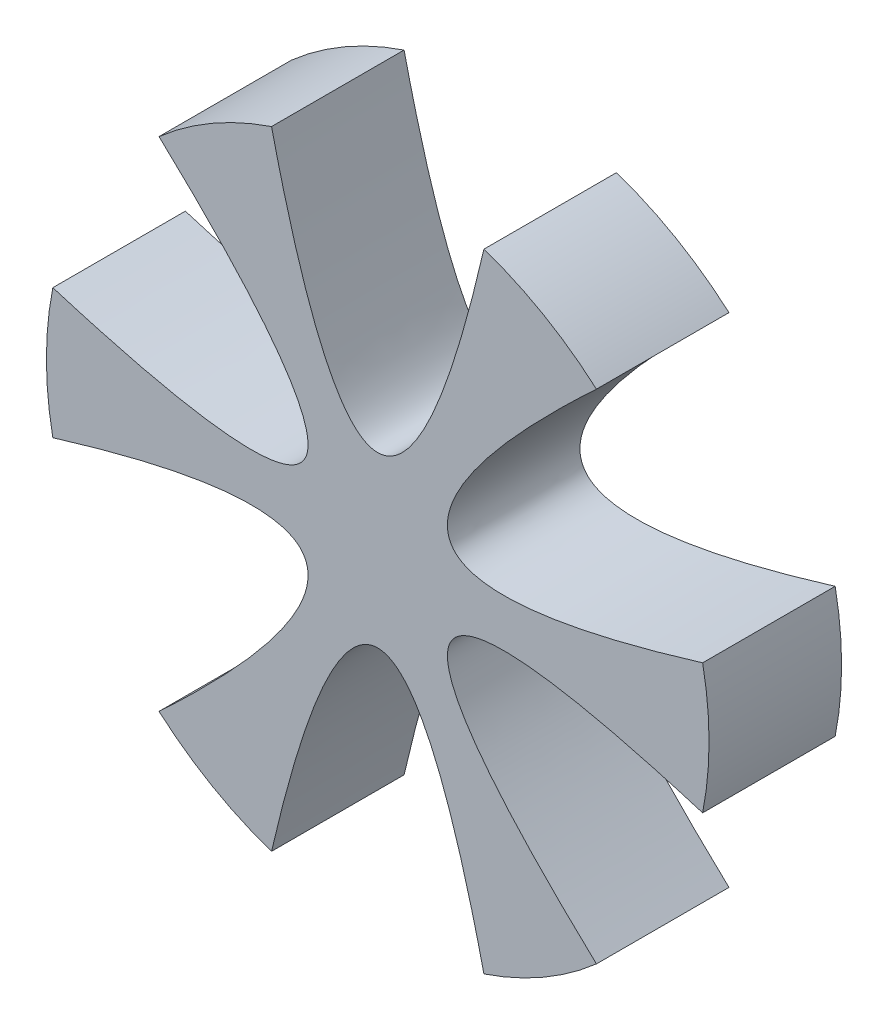
SolidWorks part; units mm, degrees
ref_plane "Front Plane" through (0, 0, 0) normal (0, 0, 1) x (1, 0, 0)
ref_plane "Top Plane" through (0, 0, 0) normal (0, 1, 0) x (1, 0, 0)
ref_plane "Right Plane" through (0, 0, 0) normal (1, 0, 0) x (0, 0, -1)
sketch "Sketch2" plane through (0, 0, 0) normal (0, 0, 1) x (1, 0, 0)
  circle A0 centre (0, 0) radius 38.1
  dimension "D1" = 76.2
extrude "Boss-Extrude1" add sketch "Sketch2" along normal blind 2.54
sketch "Sketch3" plane through (0, 0, 2.54) normal (0, 0, 1) x (1, 0, 0)
  line L0 (0, 0) -> (0, 57.9417) construction
  arc A0 (-37.3604, 7.4707) -> (-37.3604, -7.4707) centre (0, 0) ccw
  arc A1 (-12.2104, 36.0904) -> (-25.15, 28.6197) centre (0, 0) ccw
  circle A2 centre (0, 0) radius 38.1 construction
  arc A3 (25.15, 28.6197) -> (12.2104, 36.0904) centre (0, 0) ccw
  arc A4 (37.3604, -7.4707) -> (37.3604, 7.4707) centre (0, 0) ccw
  arc A5 (12.2104, -36.0904) -> (25.15, -28.6197) centre (0, 0) ccw
  arc A6 (-25.15, -28.6197) -> (-12.2104, -36.0904) centre (0, 0) ccw
  spline S0 degree 2 poles (-12.2104, 36.0904) (0, -16.6414) (12.2104, 36.0904) knots 0 0 0 1 1 1
  spline S1 degree 2 poles (25.15, 28.6197) (-14.4119, -8.3207) (37.3604, 7.4707) knots 0 0 0 1 1 1
  spline S2 degree 2 poles (37.3604, -7.4707) (-14.4119, 8.3207) (25.15, -28.6197) knots 0 0 0 1 1 1
  spline S3 degree 2 poles (12.2104, -36.0904) (0, 16.6414) (-12.2104, -36.0904) knots 0 0 0 1 1 1
  spline S4 degree 2 poles (-25.15, -28.6197) (14.4119, 8.3207) (-37.3604, -7.4707) knots 0 0 0 1 1 1
  spline S5 degree 2 poles (-37.3604, 7.4707) (14.4119, -8.3207) (-25.15, 28.6197) knots 0 0 0 1 1 1
  point P25 (0, 0)
extrude "Boss-Extrude2" add sketch "Sketch3" along normal blind 12.7
sketch "Sketch4" plane through (0, 0, 0) normal (0, 0, -1) x (-1, 0, 0)
  circle A0 centre (0, 0) radius 1.524
  dimension "D1" = 3.048
extrude "Cut-Extrude1" cut sketch "Sketch4" against normal blind 3.81
sketch "Sketch6" plane through (0, 0, 15.24) normal (0, 0, 1) x (1, 0, 0)
  arc A0 (-37.3604, -7.4707) -> (-25.15, -28.6197) centre (0, 0) ccw construction
  arc A1 (-25.15, 28.6197) -> (-37.3604, 7.4707) centre (0, 0) ccw construction
  arc A2 (12.2104, 36.0904) -> (-12.2104, 36.0904) centre (0, 0) ccw construction
  arc A3 (37.3604, 7.4707) -> (25.15, 28.6197) centre (0, 0) ccw construction
  arc A4 (-12.2104, -36.0904) -> (12.2104, -36.0904) centre (0, 0) ccw construction
  arc A5 (25.15, -28.6197) -> (37.3604, -7.4707) centre (0, 0) ccw construction
  arc A6 (-37.3604, -7.4707) -> (-25.15, -28.6197) centre (0, 0) ccw
  arc A7 (-25.15, 28.6197) -> (-37.3604, 7.4707) centre (0, 0) ccw
  arc A8 (12.2104, 36.0904) -> (-12.2104, 36.0904) centre (0, 0) ccw
  arc A9 (37.3604, 7.4707) -> (25.15, 28.6197) centre (0, 0) ccw
  arc A10 (-12.2104, -36.0904) -> (12.2104, -36.0904) centre (0, 0) ccw
  arc A11 (25.15, -28.6197) -> (37.3604, -7.4707) centre (0, 0) ccw
  parabola Q0 (-25.15, 28.6197) -> (-37.3604, 7.4707) focus (-9.646, 5.5691) apex (-8.4217, 4.8622) construction
  parabola Q1 (37.3604, 7.4707) -> (25.15, 28.6197) focus (9.646, 5.5691) apex (8.4217, 4.8622) construction
  parabola Q2 (25.15, -28.6197) -> (37.3604, -7.4707) focus (9.646, -5.5691) apex (8.4217, -4.8622) construction
  parabola Q3 (-25.15, 28.6197) -> (-37.3604, 7.4707) focus (-9.646, 5.5691) apex (-8.4217, 4.8622)
  parabola Q4 (37.3604, 7.4707) -> (25.15, 28.6197) focus (9.646, 5.5691) apex (8.4217, 4.8622)
  parabola Q5 (25.15, -28.6197) -> (37.3604, -7.4707) focus (9.646, -5.5691) apex (8.4217, -4.8622)
  spline M5 degree 2 poles (12.2104, 36.0904) (0, -16.6414) (-12.2104, 36.0904) knots 0 0 0 1 1 1
  spline M7 degree 2 poles (-25.15, 28.6197) (14.4119, -8.3207) (-37.3604, 7.4707) knots 0 0 0 1 1 1
  spline M9 degree 2 poles (-37.3604, -7.4707) (14.4119, 8.3207) (-25.15, -28.6197) knots 0 0 0 1 1 1
  spline M11 degree 2 poles (-12.2104, -36.0904) (0, 16.6414) (12.2104, -36.0904) knots 0 0 0 1 1 1
  spline M13 degree 2 poles (25.15, -28.6197) (-14.4119, 8.3207) (37.3604, -7.4707) knots 0 0 0 1 1 1
  spline M15 degree 2 poles (37.3604, 7.4707) (-14.4119, -8.3207) (25.15, 28.6197) knots 0 0 0 1 1 1
extrude "Cut-Extrude2" cut sketch "Sketch6" against normal blind 46.228 contours A11 M13 | A9 M15 | A8 M5 | A7 M7 | A6 M9 | A10 M11
